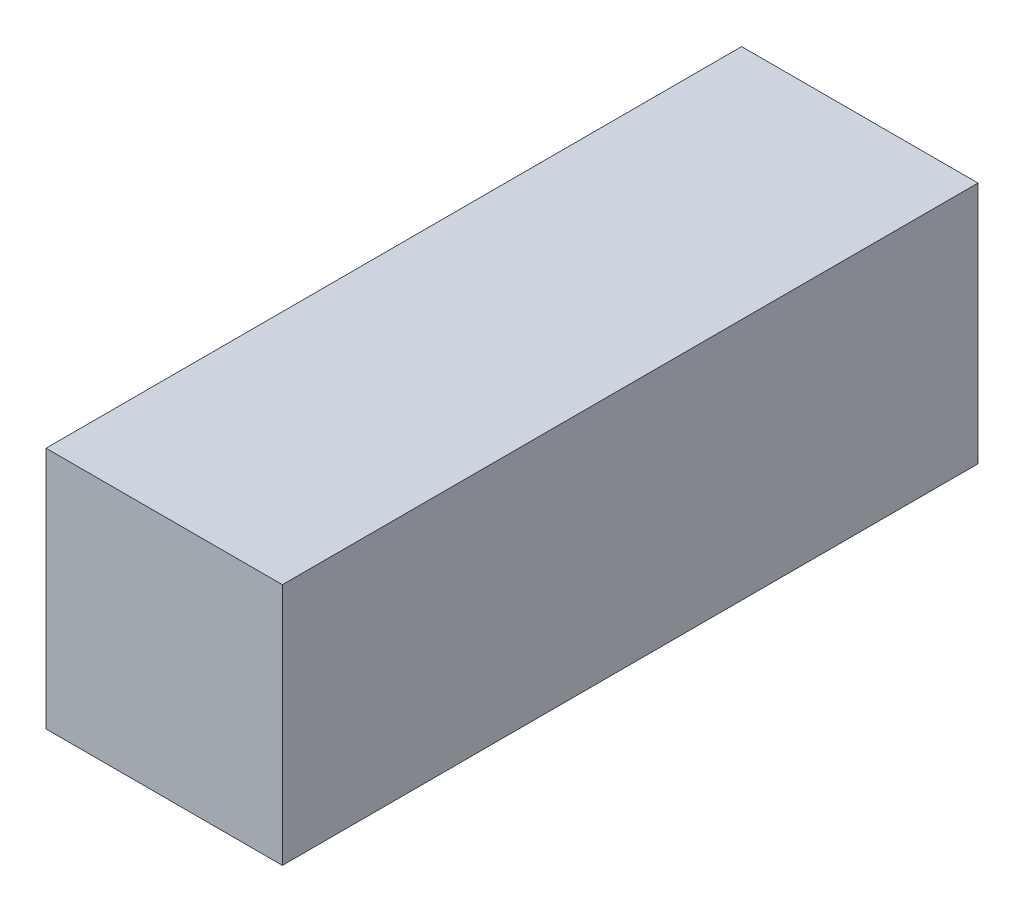
SolidWorks part; units mm, degrees
ref_plane "Front Plane" through (0, 0, 0) normal (0, 0, 1) x (1, 0, 0)
ref_plane "Top Plane" through (0, 0, 0) normal (0, 1, 0) x (1, 0, 0)
ref_plane "Right Plane" through (0, 0, 0) normal (1, 0, 0) x (0, 0, -1)
sketch "Sketch1" plane through (0, 0, 0) normal (0, 0, 1) x (1, 0, 0)
  line L1 (-17.5, -18) -> (17.5, -18)
  line L2 (-17.5, -18) -> (-17.5, 18)
  line L3 (-17.5, 18) -> (17.5, 18)
  line L4 (17.5, -18) -> (17.5, 18)
  line L5 (-17.5, -18) -> (17.5, 18) construction
  line L6 (-17.5, 18) -> (17.5, -18) construction
  point P0 (0, 0)
  dimension "D1" = 35
  dimension "D2" = 36
extrude "Boss-Extrude1" add sketch "Sketch1" along normal blind 103
